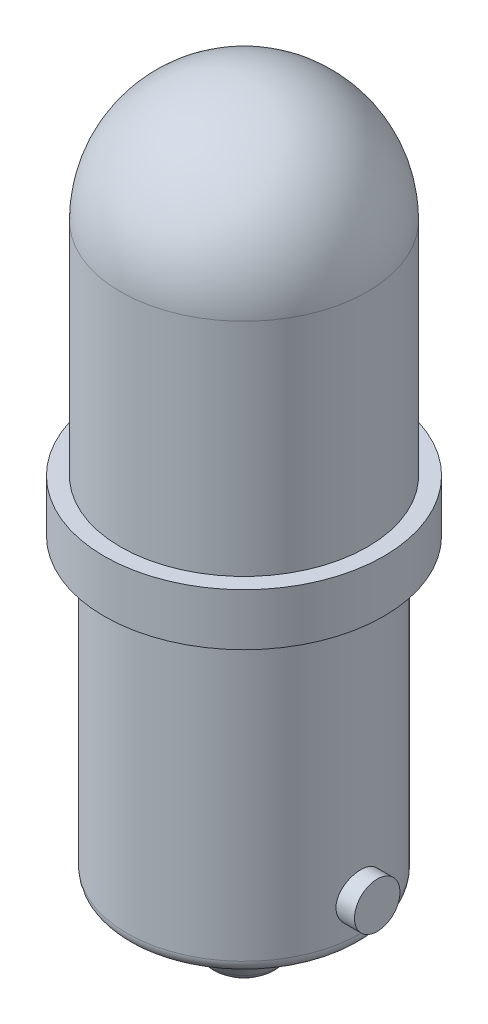
SolidWorks part; units mm, degrees
ref_plane "Front Plane" through (0, 0, 0) normal (0, 0, 1) x (1, 0, 0)
ref_plane "Top Plane" through (0, 0, 0) normal (0, 1, 0) x (1, 0, 0)
ref_plane "Right Plane" through (0, 0, 0) normal (1, 0, 0) x (0, 0, -1)
sketch "Sketch2" plane through (0, 0, 0) normal (0, 1, 0) x (1, 0, 0)
  circle A0 centre (0, 0) radius 4.826
  dimension "D1" = 9.652
extrude "Boss-Extrude1" add sketch "Sketch2" along normal blind 15.494
fillet "Fillet1" radius 4.826 1 edges at (0, 15.494, 4.826)
sketch "Sketch3" plane through (0, 0, 0) normal (0, -1, 0) x (1, 0, 0)
  circle A0 centre (0, 0) radius 5.461
  dimension "D1" = 10.922
extrude "Boss-Extrude2" add sketch "Sketch3" against normal blind 2.032
sketch "Sketch4" plane through (0, 0, 0) normal (0, -1, 0) x (1, 0, 0)
  circle A0 centre (0, 0) radius 4.572
  dimension "D1" = 9.144
extrude "Boss-Extrude3" add sketch "Sketch4" along normal blind 11.684
sketch "Sketch5" plane through (0, -11.684, 0) normal (0, -1, 0) x (1, 0, 0)
  circle A0 centre (0, 0) radius 2.921
  dimension "D1" = 5.842
extrude "Boss-Extrude4" add sketch "Sketch5" along normal blind 2.794 draft 35
fillet "Fillet2" radius 1.27 1 edges at (0, -14.478, -0.9646)
fillet "Fillet3" radius 0.508 1 edges at (0, -11.684, -4.572)
sketch "Sketch6" plane through (0, 0, 0) normal (1, 0, 0) x (0, 0, -1)
  line L0 (0, 6.0071) -> (0, -6.0071) construction
  line L1 (6.0071, 0) -> (-6.0071, 0) construction
  circle A0 centre (0, -9.906) radius 0.889
  dimension "D2" = 1.778
  dimension "D1" = 9.906
extrude "Boss-Extrude5" add sketch "Sketch6" along normal mid plane 10.414
